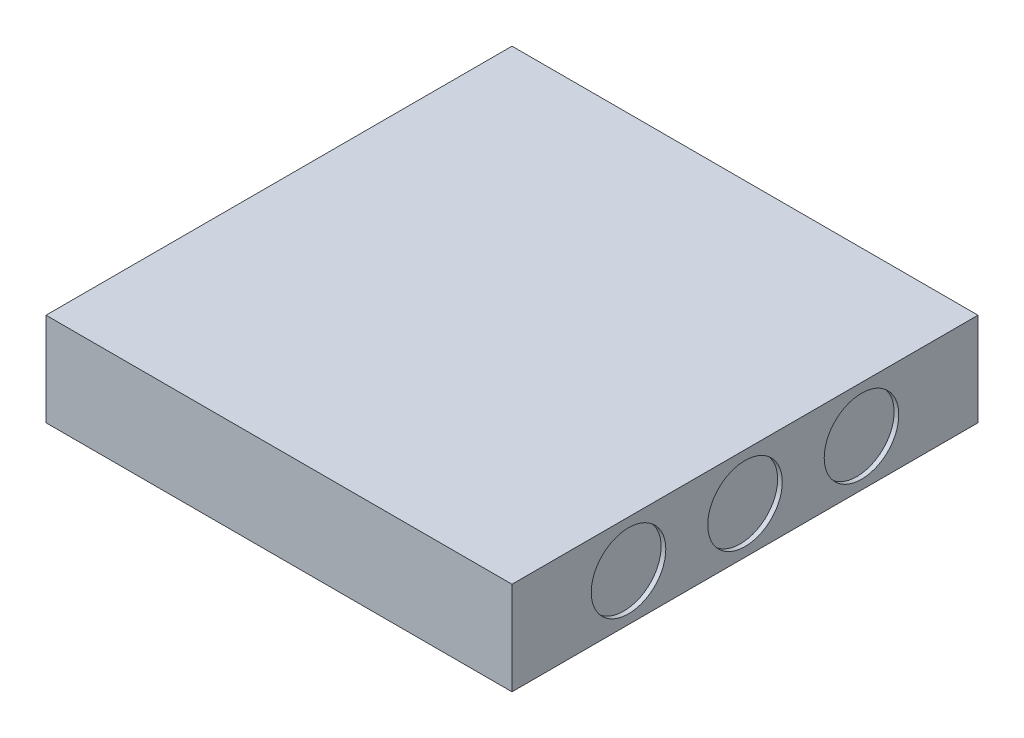
SolidWorks part; units mm, degrees
ref_plane "Front Plane" through (0, 0, 0) normal (0, 0, 1) x (1, 0, 0)
ref_plane "Top Plane" through (0, 0, 0) normal (0, 1, 0) x (1, 0, 0)
ref_plane "Right Plane" through (0, 0, 0) normal (1, 0, 0) x (0, 0, -1)
sketch "Sketch1" plane through (0, 0, 0) normal (0, 1, 0) x (1, 0, 0)
  line L1 (-25, -25) -> (25, -25)
  line L2 (-25, -25) -> (-25, 25)
  line L3 (-25, 25) -> (25, 25)
  line L4 (25, -25) -> (25, 25)
  line L5 (-25, -25) -> (25, 25) construction
  line L6 (-25, 25) -> (25, -25) construction
  point P0 (0, 0)
extrude "Boss-Extrude1" add sketch "Sketch1" along normal blind 10
sketch "Sketch2" plane through (-25, 0, 0) normal (-1, 0, 0) x (0, 0, 1)
  line L0 (-25, 10) -> (25, 0) construction
  line L1 (-25, 0) -> (25, 10) construction
  line L3 (-2.5, 7.5) -> (2.5, 7.5)
  line L4 (-2.5, 7.5) -> (-2.5, 2.5)
  line L5 (-2.5, 2.5) -> (2.5, 2.5)
  line L6 (2.5, 7.5) -> (2.5, 2.5)
  line L7 (-2.5, 7.5) -> (2.5, 2.5) construction
  line L8 (-2.5, 2.5) -> (2.5, 7.5) construction
  point P8 (0, 5)
extrude "Cut-Extrude1" cut sketch "Sketch2" against normal blind 6
sketch "Sketch3" plane through (25, 0, 0) normal (1, 0, 0) x (0, 0, -1)
  line L0 (-25, 10) -> (25, 0) construction
  line L4 (0, 10) -> (0, 0) construction
  line L5 (-25, 10) -> (25, 10) construction
  line L6 (-25, 0) -> (25, 0) construction
  circle A0 centre (-12.5, 5) radius 4
  circle A1 centre (12.5, 5) radius 4
  circle A2 centre (0, 5) radius 4
extrude "Cut-Extrude2" cut sketch "Sketch3" against normal blind 0.5
